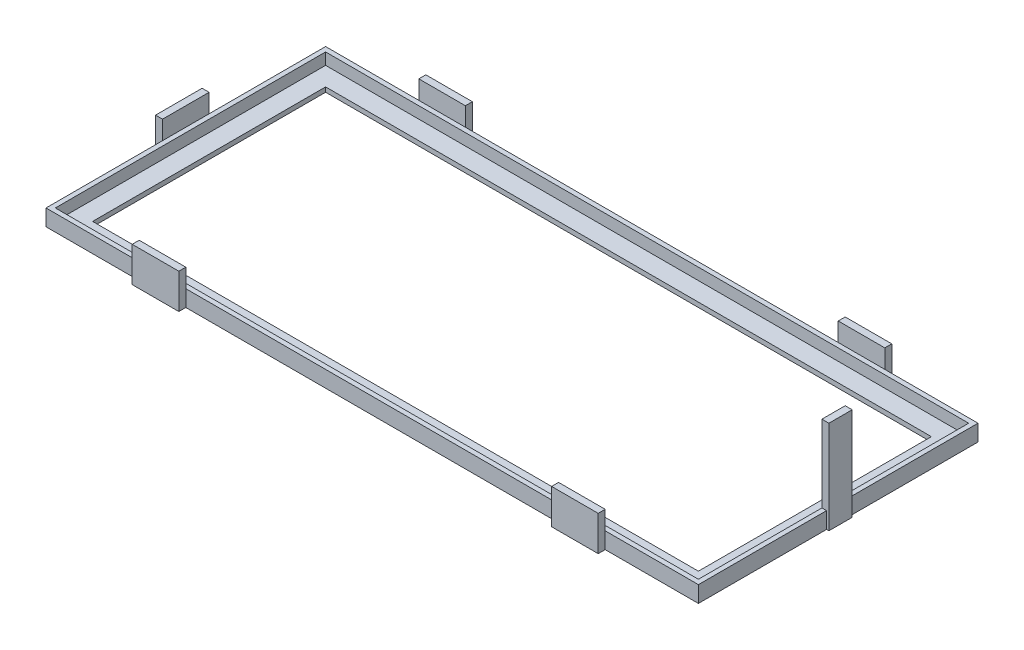
SolidWorks part; units mm, degrees
ref_plane "Front" through (0, 0, 0) normal (0, 0, 1) x (1, 0, 0)
ref_plane "Top" through (0, 0, 0) normal (0, 1, 0) x (1, 0, 0)
ref_plane "Right" through (0, 0, 0) normal (1, 0, 0) x (0, 0, -1)
sketch "Sketch1" plane through (0, 0, 0) normal (0, 1, 0) x (1, 0, 0)
  line L1 (0, 0) -> (280, 0)
  line L2 (0, 0) -> (0, -120)
  line L3 (0, -120) -> (280, -120)
  line L4 (280, 0) -> (280, -120)
  dimension "D1" = 120
  dimension "D2" = 280
extrude "Boss-Extrude1" add sketch "Sketch1" along normal blind 2
sketch "Sketch2" plane through (0, 2, 0) normal (0, 1, 0) x (1, 0, 0)
  line L0 (2, -118) -> (2, -2)
  line L1 (0, -120) -> (280, -120)
  line L2 (0, -120) -> (0, 0)
  line L3 (0, 0) -> (280, 0)
  line L4 (280, -120) -> (280, 0)
  line L5 (2, -2) -> (278, -2)
  line L6 (278, -118) -> (278, -2)
  line L7 (2, -118) -> (278, -118)
  dimension "D1" = 2
extrude "Boss-Extrude2" add sketch "Sketch2" along normal blind 5
sketch "Sketch4" plane through (0, 0, 0) normal (0, -1, 0) x (-1, 0, 0)
  line L0 (-280, 0) -> (0, 0) construction
  line L1 (-40, 0) -> (-60, 0)
  line L2 (-40, 0) -> (-40, 3)
  line L3 (-40, 3) -> (-60, 3)
  line L4 (-60, 0) -> (-60, 3)
  line L5 (0, 0) -> (0, -120) construction
  line L6 (-220, 3) -> (-240, 3)
  line L7 (-220, 0) -> (-220, 3)
  line L8 (-240, 0) -> (-240, 3)
  line L9 (-220, 0) -> (-240, 0)
  line L10 (-220, -120) -> (-240, -120)
  line L11 (-220, -123) -> (-220, -120)
  line L12 (-240, -123) -> (-240, -120)
  line L13 (-220, -123) -> (-240, -123)
  line L14 (-40, -120) -> (-60, -120)
  line L15 (-40, -123) -> (-40, -120)
  line L16 (-60, -123) -> (-60, -120)
  line L17 (-40, -123) -> (-60, -123)
  line L19 (0, -50) -> (3, -50)
  line L20 (0, -50) -> (0, -70)
  line L21 (0, -70) -> (3, -70)
  line L22 (3, -50) -> (3, -70)
  dimension "D1" = 3
  dimension "D2" = 20
  dimension "D3" = 40
  dimension "D6" = 20
  dimension "D7" = 3
  dimension "D8" = 50
  dimension "D4" = 2
  dimension "D5" = 2
extrude "Boss-Extrude3" add sketch "Sketch4" against normal blind 15
sketch "Sketch5" plane through (0, 0, 0) normal (0, -1, 0) x (-1, 0, 0)
  line L0 (-280, 0) -> (-240, 0) construction
  line L1 (-278, -55) -> (-281, -55)
  line L2 (-278, -55) -> (-278, -65)
  line L3 (-278, -65) -> (-281, -65)
  line L4 (-281, -55) -> (-281, -65)
  line L5 (-280, -120) -> (-280, 0) construction
  dimension "D1" = 10
  dimension "D2" = 55
  dimension "D3" = 3
  dimension "D4" = 2
extrude "Boss-Extrude4" add sketch "Sketch5" against normal blind 40
sketch "Sketch6" plane through (0, 0, 0) normal (0, -1, 0) x (-1, 0, 0)
  line L0 (-10, -110) -> (-10, -10)
  line L5 (-10, -10) -> (-270, -10)
  line L6 (-270, -110) -> (-270, -10)
  line L7 (-10, -110) -> (-270, -110)
extrude "Cut-Extrude2" cut sketch "Sketch6" against normal through all
